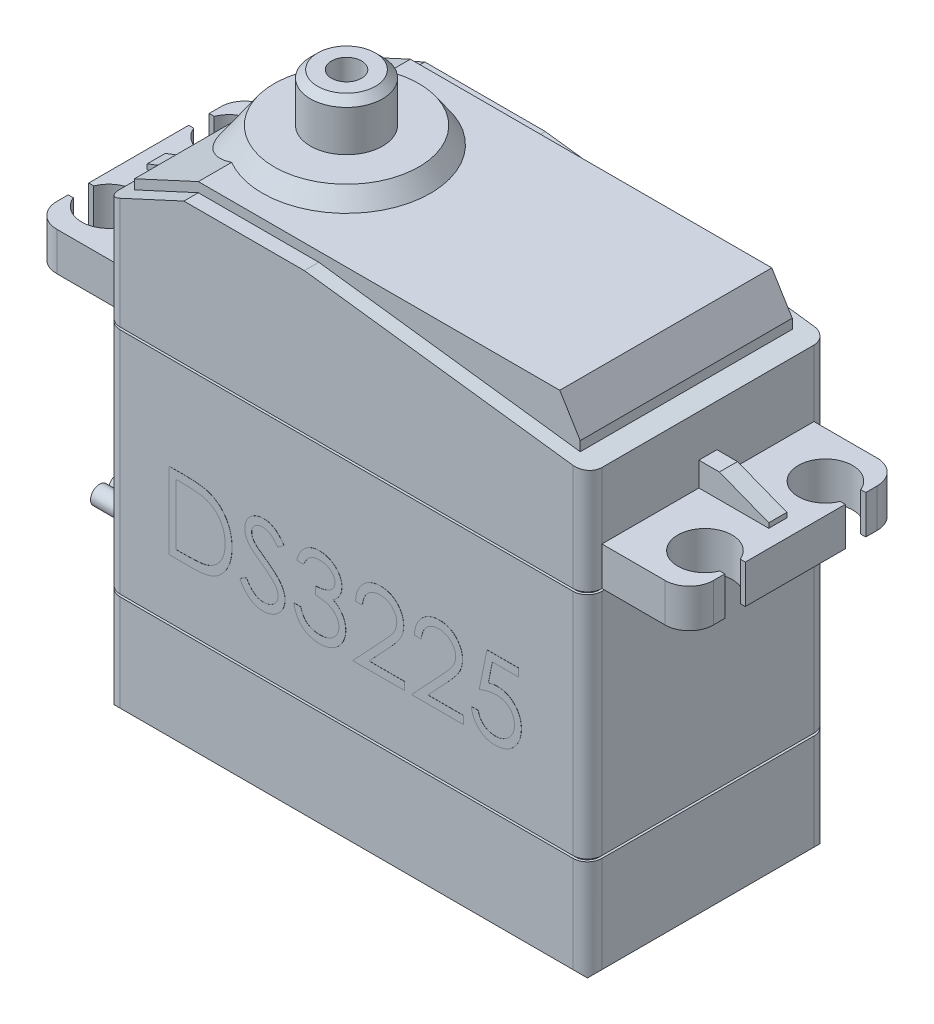
SolidWorks part; units mm, degrees
ref_plane "Front" through (0, 0, 0) normal (0, 0, 1) x (1, 0, 0)
ref_plane "Top" through (0, 0, 0) normal (0, 1, 0) x (1, 0, 0)
ref_plane "Right" through (0, 0, 0) normal (1, 0, 0) x (0, 0, -1)
sketch "Sketch1" plane through (0, 0, 0) normal (0, 1, 0) x (1, 0, 0)
  line L1 (-20, -10) -> (20, -10)
  line L2 (-20, -10) -> (-20, 10)
  line L3 (-20, 10) -> (20, 10)
  line L4 (20, -10) -> (20, 10)
  line L5 (-20, -10) -> (20, 10) construction
  line L6 (-20, 10) -> (20, -10) construction
  point P0 (0, 0)
  dimension "D1" = 20
  dimension "D2" = 40
extrude "Boss-Extrude1" add sketch "Sketch1" along normal blind 41.5
chamfer "Chamfer1" distance 1.6 angle 45 4 edges at (0, 0, -10) (-20, 0, 0) (0, 0, 10) (20, 0, 0)
fillet "Fillet2" radius 1.2 4 edges at (20, 21.55, 10) (20, 21.55, -10) (-20, 21.55, -10) (-20, 21.55, 10)
ref_plane "Plane1" through (0, 29, 0) normal (0, -1, 0) x (-1, 0, 0)
sketch "Sketch3" plane through (0, 29, 0) normal (0, -1, 0) x (-1, 0, 0)
  line L0 (20, 8.8) -> (20, -8.8) construction
  line L1 (-20, -8.8) -> (-20, 8.8) construction
  line L2 (20, 8.8) -> (20, -8.8)
  line L3 (-20, -8.8) -> (-20, 8.8)
  line L4 (-27.25, 5) -> (27.25, 5) construction
  line L5 (-25.25, -8.8) -> (25.25, -8.8)
  line L6 (-27.25, -6.8) -> (-27.25, 6.8)
  line L7 (-25.25, 8.8) -> (25.25, 8.8)
  line L8 (27.25, -6.8) -> (27.25, 6.8)
  line L9 (-27.25, -8.8) -> (27.25, 8.8) construction
  line L10 (-27.25, 8.8) -> (27.25, -8.8) construction
  line L11 (-27.25, 4.15) -> (27.25, 4.15)
  line L12 (-27.25, 5.85) -> (27.25, 5.85)
  line L13 (-27.25, -5) -> (27.25, -5) construction
  line L14 (-27.25, -5.85) -> (27.25, -5.85)
  line L15 (-27.25, -4.15) -> (27.25, -4.15)
  arc A0 (27.25, -6.8) -> (25.25, -8.8) centre (25.25, -6.8) cw
  arc A1 (27.25, 6.8) -> (25.25, 8.8) centre (25.25, 6.8) ccw
  arc A2 (-25.25, -8.8) -> (-27.25, -6.8) centre (-25.25, -6.8) cw
  arc A3 (-25.25, 8.8) -> (-27.25, 6.8) centre (-25.25, 6.8) ccw
  circle A4 centre (-24.75, 5) radius 2.25
  circle A5 centre (24.75, 5) radius 2.25
  circle A6 centre (-24.75, -5) radius 2.25
  circle A7 centre (24.75, -5) radius 2.25
  point P4 (0, 0)
  dimension "D3" = 2
  dimension "D4" = 4.5
  dimension "D5" = 4.5
  dimension "D8" = 4.5
  dimension "D9" = 4.5
  dimension "D1" = 17.6
  dimension "D2" = 54.5
  dimension "D6" = 49.5
  dimension "D7" = 24.75
  dimension "D10" = 10
  dimension "D11" = 5
  dimension "D12" = 0.85
  dimension "D14" = 0.85
  dimension "D13" = 0.85
  dimension "D15" = 0.85
extrude "Boss-Extrude3" add sketch "Sketch3" against normal blind 3.2 contours A5 L12 L8 A1 L7 L2 | A7 L15 L8 L11 A5 L2 | A7 L14 L2 L5 A0 L8 | A7 L15 L2 L14 | A5 L12 L2 L11 | A4 L12 L3 L7 A3 L6 | A4 L11 L3 L12 | A6 L15 L3 L11 A4 L6 | A6 L14 L3 L15 | A6 L14 L6 A2 L5 L3
sketch "Sketch4" plane through (0, 0, 10) normal (0, 0, 1) x (1, 0, 0)
  line L0 (-20, 37.7) -> (-13.5, 40.7)
  line L1 (-20, 32.2) -> (-20, 41.5) construction
  line L2 (-13.5, 40.7) -> (-3.5, 40.7)
  line L3 (-3.5, 40.7) -> (20, 37.7)
  line L4 (20, 41.5) -> (20, 32.2) construction
  line L5 (20, 37.7) -> (20, 41.5)
  line L6 (20, 41.5) -> (-20, 41.5)
  line L7 (-20, 41.5) -> (-20, 37.7)
  dimension "D1" = 3.8
  dimension "D2" = 3.8
  dimension "D3" = 0.8
  dimension "D4" = 10
  dimension "D5" = 6.5
extrude "Cut-Extrude1" cut sketch "Sketch4" against normal up to next
sketch "Sketch5" plane through (0, 0, 0) normal (0, 0, 1) x (1, 0, 0)
  line L0 (-13.5, 41.5) -> (16.5, 41.5)
  line L1 (16.5, 41.5) -> (18.2, 38.7298)
  line L2 (18.2, 38.7298) -> (18.2, 37.9298)
  line L3 (-3.5, 40.7) -> (18.8, 37.8532) construction
  line L4 (18.2, 37.9298) -> (-3.5, 40.7)
  line L5 (-3.5, 40.7) -> (-13.5, 40.7)
  line L6 (-13.5, 40.7) -> (-18.8, 38.2538)
  line L7 (-18.8, 38.2538) -> (-13.5, 40.7) construction
  line L8 (-18.8, 38.2538) -> (-18.8, 39.0538)
  line L9 (-18.8, 39.0538) -> (-13.5, 41.5)
  line L10 (-20, 32.2) -> (-20, 37.7) construction
  line L11 (20, 37.7) -> (20, 32.2) construction
  point P14 (-18.8, 38.6538)
  dimension "D1" = 0.8
  dimension "D2" = 1.2
  dimension "D3" = 1.8
  dimension "D4" = 0.8
  dimension "D5" = 30
extrude "Boss-Extrude4" add sketch "Sketch5" along normal mid plane 17.6
ref_plane "Plane2" through (0, 42.9, 0) normal (0, 1, 0) x (1, 0, 0)
sketch "Sketch6" plane through (0, 42.9, 0) normal (0, 1, 0) x (1, 0, 0)
  line L0 (-27.25, -4.15) -> (-27.25, 4.15) construction
  circle A0 centre (-10, 0) radius 6
  dimension "D1" = 12
  dimension "D2" = 17.25
extrude "Boss-Extrude5" add sketch "Sketch6" against normal up to next draft 35 draft outward yes
sketch "Sketch7" plane through (0, 42.9, 0) normal (0, 1, 0) x (1, 0, 0)
  circle A0 centre (-10, 0) radius 3
  circle A1 centre (-10, 0) radius 1.25
  dimension "D1" = 6
  dimension "D2" = 2.5
extrude "Boss-Extrude6" add sketch "Sketch7" along normal blind 4
chamfer "Chamfer2" distance 0.6 angle 45 1 edges at (-10, 46.9, 3)
sketch "Sketch8" plane through (0, 0, 0) normal (0, 0, 1) x (1, 0, 0)
  line L0 (-20, 34.2) -> (-21.7, 34.2)
  line L1 (-20, 32.2) -> (-20, 37.7) construction
  line L2 (-21.7, 34.2) -> (-25.8, 32.6)
  line L3 (-25.8, 32.6) -> (-25.8, 32.2)
  line L4 (-20, 32.2) -> (-25.25, 32.2) construction
  line L5 (-25.8, 32.2) -> (-20, 32.2)
  line L6 (-20, 32.2) -> (-20, 34.2)
  line L7 (0, 0) -> (0, 11.9728) construction
  line L8 (20, 32.2) -> (20, 34.2)
  line L9 (25.8, 32.2) -> (20, 32.2)
  line L10 (25.8, 32.6) -> (25.8, 32.2)
  line L11 (21.7, 34.2) -> (25.8, 32.6)
  line L12 (20, 34.2) -> (21.7, 34.2)
  dimension "D1" = 5.8
  dimension "D2" = 1.7
  dimension "D3" = 2
  dimension "D4" = 0.4
extrude "Boss-Extrude7" add sketch "Sketch8" along normal mid plane 1.5
ref_plane "Plane3" through (0, 9.6, 0) normal (0, -1, 0) x (-1, 0, 0)
sketch "Sketch9" plane through (0, 9.6, 0) normal (0, -1, 0) x (-1, 0, 0)
  line L0 (20, 8.8) -> (20, -8.8) construction
  line L1 (18.8, -10) -> (-18.8, -10) construction
  line L2 (-20, -8.8) -> (-20, 8.8) construction
  line L3 (-18.8, 10) -> (18.8, 10) construction
  line L4 (20, 8.8) -> (20, -8.8)
  line L5 (18.8, -10) -> (-18.8, -10)
  line L6 (-20, -8.8) -> (-20, 8.8)
  line L7 (-18.8, 10) -> (18.8, 10)
  line L8 (-18.8, 9.8) -> (18.8, 9.8)
  line L9 (19.8, 8.8) -> (19.8, -8.8)
  line L10 (18.8, -9.8) -> (-18.8, -9.8)
  line L11 (-19.8, -8.8) -> (-19.8, 8.8)
  arc A0 (19.6485, 9.6485) -> (18.8, 10) centre (18.8, 8.8) ccw construction
  arc A1 (20, 8.8) -> (19.6485, 9.6485) centre (18.8, 8.8) ccw construction
  arc A2 (19.6485, -9.6485) -> (20, -8.8) centre (18.8, -8.8) ccw construction
  arc A3 (18.8, -10) -> (19.6485, -9.6485) centre (18.8, -8.8) ccw construction
  arc A4 (-19.6485, -9.6485) -> (-18.8, -10) centre (-18.8, -8.8) ccw construction
  arc A5 (-20, -8.8) -> (-19.6485, -9.6485) centre (-18.8, -8.8) ccw construction
  arc A6 (-18.8, 10) -> (-19.6485, 9.6485) centre (-18.8, 8.8) ccw construction
  arc A7 (-19.6485, 9.6485) -> (-20, 8.8) centre (-18.8, 8.8) ccw construction
  arc A8 (19.6485, 9.6485) -> (18.8, 10) centre (18.8, 8.8) ccw
  arc A9 (20, 8.8) -> (19.6485, 9.6485) centre (18.8, 8.8) ccw
  arc A10 (19.6485, -9.6485) -> (20, -8.8) centre (18.8, -8.8) ccw
  arc A11 (18.8, -10) -> (19.6485, -9.6485) centre (18.8, -8.8) ccw
  arc A12 (-19.6485, -9.6485) -> (-18.8, -10) centre (-18.8, -8.8) ccw
  arc A13 (-20, -8.8) -> (-19.6485, -9.6485) centre (-18.8, -8.8) ccw
  arc A14 (-18.8, 10) -> (-19.6485, 9.6485) centre (-18.8, 8.8) ccw
  arc A15 (-19.6485, 9.6485) -> (-20, 8.8) centre (-18.8, 8.8) ccw
  arc A16 (19.5071, 9.5071) -> (18.8, 9.8) centre (18.8, 8.8) ccw
  arc A17 (19.8, 8.8) -> (19.5071, 9.5071) centre (18.8, 8.8) ccw
  arc A18 (19.5071, -9.5071) -> (19.8, -8.8) centre (18.8, -8.8) ccw
  arc A19 (18.8, -9.8) -> (19.5071, -9.5071) centre (18.8, -8.8) ccw
  arc A20 (-19.5071, -9.5071) -> (-18.8, -9.8) centre (-18.8, -8.8) ccw
  arc A21 (-19.8, -8.8) -> (-19.5071, -9.5071) centre (-18.8, -8.8) ccw
  arc A22 (-19.5071, 9.5071) -> (-19.8, 8.8) centre (-18.8, 8.8) ccw
  arc A23 (-18.8, 9.8) -> (-19.5071, 9.5071) centre (-18.8, 8.8) ccw
  dimension "D1" = 0.2
extrude "Cut-Extrude2" cut sketch "Sketch9" against normal blind 0.2
pattern_linear "LPattern1" count 2 spacing 19.2 along (0, 1, 0) of "Cut-Extrude2"
sketch "Sketch10" plane through (-20, 0, 0) normal (-1, 0, 0) x (0, 0, 1)
  line L0 (8.8, 9.6) -> (-8.8, 9.6) construction
  line L1 (-3, 9.6) -> (3, 9.6)
  line L2 (-3.5, 9.1) -> (-3.5, 6.1)
  line L3 (-3, 5.6) -> (3, 5.6)
  line L4 (3.5, 9.1) -> (3.5, 6.1)
  line L5 (-3.5, 9.6) -> (3.5, 5.6) construction
  line L6 (-3.5, 5.6) -> (3.5, 9.6) construction
  arc A0 (-3.5, 6.1) -> (-3, 5.6) centre (-3, 6.1) ccw
  arc A1 (3, 5.6) -> (3.5, 6.1) centre (3, 6.1) ccw
  arc A2 (3, 9.6) -> (3.5, 9.1) centre (3, 9.1) cw
  arc A3 (-3, 9.6) -> (-3.5, 9.1) centre (-3, 9.1) ccw
  point P0 (0, 7.6)
  dimension "D3" = 0.5
  dimension "D1" = 4
  dimension "D2" = 7
extrude "Boss-Extrude8" add sketch "Sketch10" along normal blind 0.6
sketch "Sketch11" plane through (-20.6, 0, 0) normal (-1, 0, 0) x (0, 0, 1)
  line L4 (3.5, 7.6) -> (2.1788, 7.6) construction
  line L5 (-3.2, 5.9) -> (3.2, 5.9)
  line L6 (-3.2, 5.9) -> (-3.2, 9.3)
  line L7 (-3.2, 9.3) -> (3.2, 9.3)
  line L8 (3.2, 5.9) -> (3.2, 9.3)
  line L9 (-3.2, 5.9) -> (3.2, 9.3) construction
  line L10 (-3.2, 9.3) -> (3.2, 5.9) construction
  line L11 (3.5, 6.1) -> (3.5, 9.1) construction
  point P0 (0, 7.6)
  dimension "D1" = 3.4
  dimension "D2" = 6.4
extrude "Boss-Extrude9" add sketch "Sketch11" along normal blind 4.2 draft 5
fillet "Fillet3" radius 0.5 8 edges at (-24.8, 6.2675, 0) (-24.8, 7.6, -2.8325) (-24.8, 8.9325, 0) (-24.8, 7.6, 2.8325) (-22.7, 6.0837, -3.0163) (-22.7, 9.1163, -3.0163) (-22.7, 6.0837, 3.0163) (-22.7, 9.1163, 3.0163)
sketch "Sketch12" plane through (-24.8, 0, 0) normal (-1, 0, 0) x (0, 0, 1)
  line L0 (2.3744, 7.6) -> (-2.3744, 7.6) construction
  line L1 (2.3744, 6.7256) -> (2.3744, 8.4744) construction
  line L2 (-2.3744, 8.4744) -> (-2.3744, 6.7256) construction
  line L3 (0, 8.4744) -> (0, 7.2066) construction
  line L4 (2.3744, 8.4744) -> (-2.3744, 8.4744) construction
  circle A0 centre (-1.5, 7.6) radius 0.75
  circle A1 centre (0, 7.6) radius 0.75
  circle A2 centre (1.5, 7.6) radius 0.75
  dimension "D1" = 1.5
  dimension "D2" = 3
extrude "Boss-Extrude11" add sketch "Sketch12" along normal blind 4.2 separate body contours A0 | A1 | A2
sketch "Sketch13" plane through (0, 0, 10) normal (0, 0, 1) x (1, 0, 0)
  line L0 (-15.52, 14.6807) -> (14.3015, 14.6807) construction
  text T0 "DS3225"
extrude "Boss-Extrude12" add sketch "Sketch13" along normal blind 0.01
